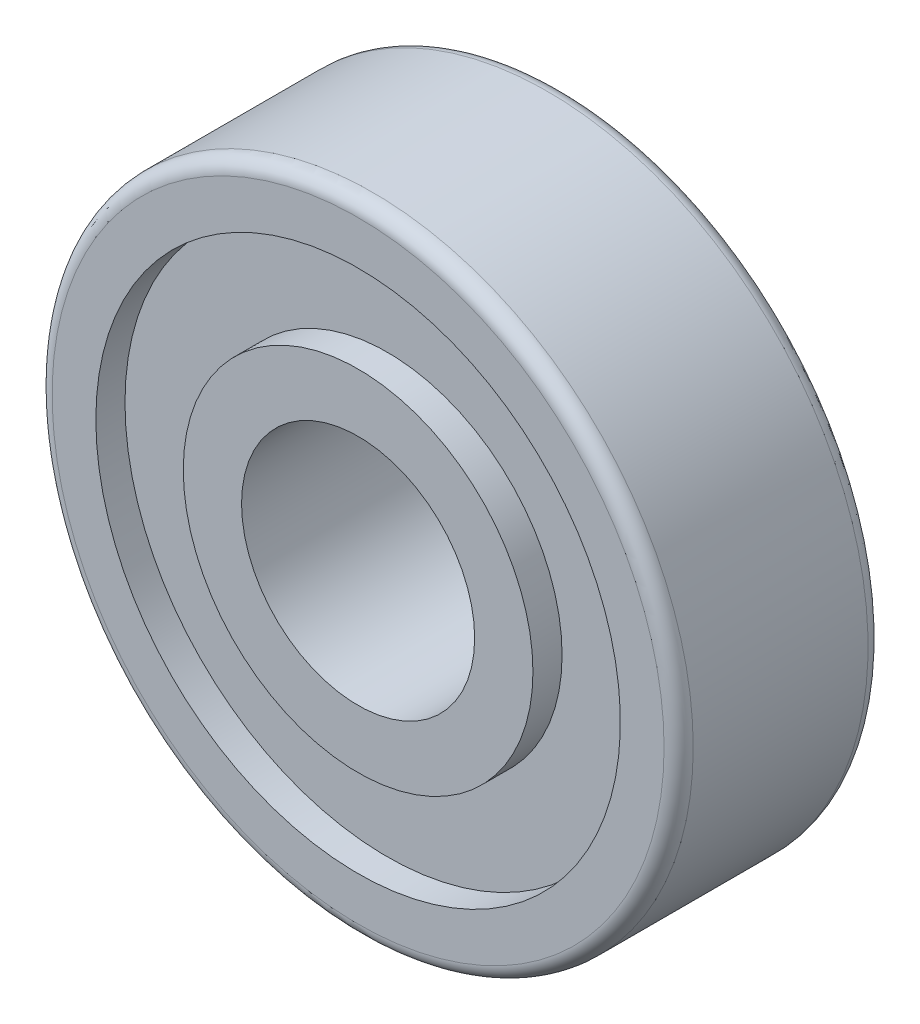
SolidWorks part; units mm, degrees
material "1060 Alloy"
ref_plane "Front Plane" through (0, 0, 0) normal (0, 0, 1) x (1, 0, 0)
ref_plane "Top Plane" through (0, 0, 0) normal (0, 1, 0) x (1, 0, 0)
ref_plane "Right Plane" through (0, 0, 0) normal (1, 0, 0) x (0, 0, -1)
ref_plane "Plane1" through (0, 0, 0) normal (0, -1, 0) x (1, 0, 0)
sketch "Sketch1" plane through (0, 0, 0) normal (0, -1, 0) x (1, 0, 0)
  line L0 (6, -3.5) -> (6, -2.5)
  line L1 (6, -2.5) -> (9, -2.5)
  line L2 (9, -2.5) -> (9, -3.5)
  line L3 (9, -3.5) -> (11, -3.5)
  line L4 (11, -3.5) -> (11, 3.5)
  line L5 (11, 3.5) -> (9, 3.5)
  line L6 (9, 3.5) -> (9, 2.5)
  line L7 (9, 2.5) -> (6, 2.5)
  line L8 (6, 2.5) -> (6, 3.5)
  line L9 (6, 3.5) -> (4, 3.5)
  line L10 (4, 3.5) -> (4, -3.5)
  line L11 (4, -3.5) -> (6, -3.5)
  line L12 (0, 3.5) -> (0, -3.5) construction
revolve "Revolve1" add sketch "Sketch1" angle 360 about L12
fillet "Fillet1" radius 0.5 2 edges at (-11, 0, -3.5) (-11, 0, 3.5)
